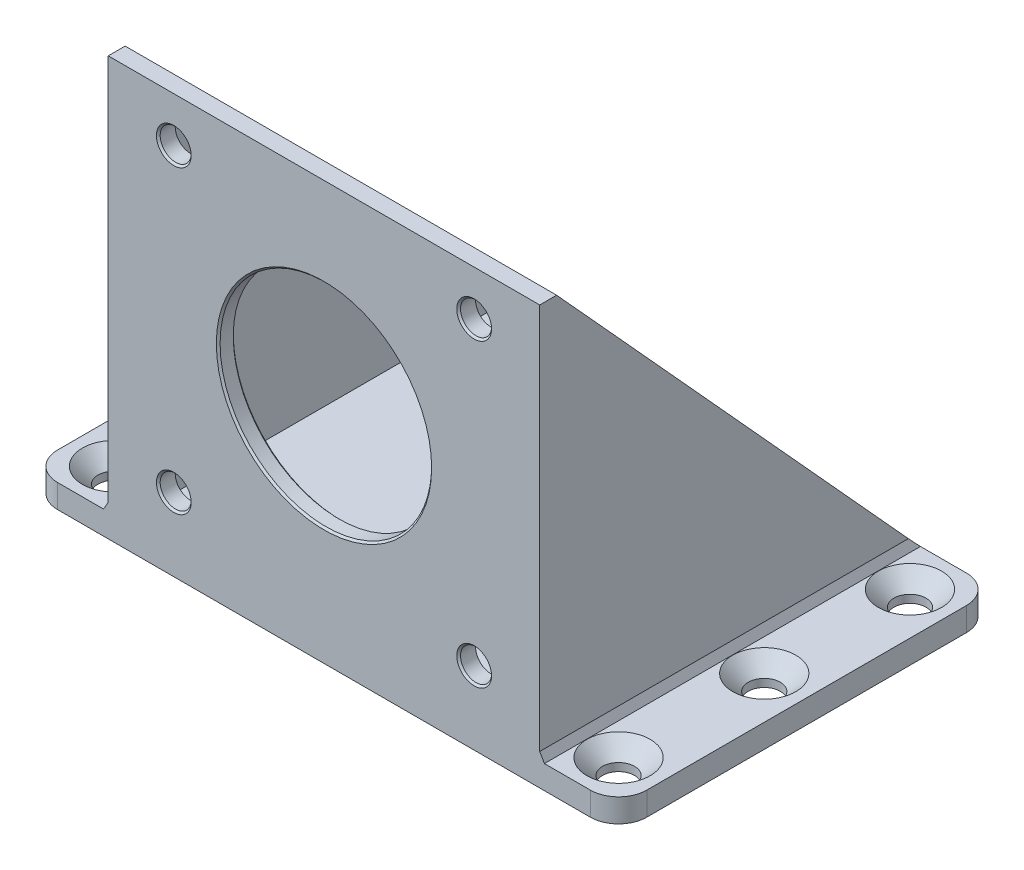
SolidWorks part; units mm, degrees
material "ABS"
ref_plane "Plano frontal" through (0, 0, 0) normal (0, 0, 1) x (1, 0, 0)
ref_plane "Plano superior" through (0, 0, 0) normal (0, 1, 0) x (1, 0, 0)
ref_plane "Plano direito" through (0, 0, 0) normal (1, 0, 0) x (0, 0, -1)
sketch "Esboço1" plane through (0, 0, 0) normal (0, 1, 0) x (1, 0, 0)
  line L1 (-28.335, -20) -> (28.335, -20)
  line L2 (-31.335, -17) -> (-31.335, 17)
  line L3 (-28.335, 20) -> (28.335, 20)
  line L4 (31.335, -17) -> (31.335, 17)
  line L5 (0, 20) -> (0, -20) construction
  line L6 (-31.335, 0) -> (31.335, 0) construction
  arc A0 (28.335, -20) -> (31.335, -17) centre (28.335, -17) ccw
  arc A1 (-31.335, 17) -> (-28.335, 20) centre (-28.335, 17) cw
  arc A2 (-28.335, -20) -> (-31.335, -17) centre (-28.335, -17) cw
  arc A3 (28.335, 20) -> (31.335, 17) centre (28.335, 17) cw
  point P0 (0, 0)
  point P9 (-31.335, 20)
  point P12 (-31.335, -20)
  point P15 (31.335, 20)
  dimension "D3" = 3
  dimension "D1" = 62.67
  dimension "D2" = 40
extrude "Ressalto-extrusão1" add sketch "Esboço1" along normal mid plane 2.5
sketch "Esboço2" plane through (0, 1.25, 0) normal (0, 1, 0) x (1, 0, 0)
  line L0 (-22.95, -20) -> (22.95, -20)
  line L1 (-21.15, 18.2) -> (21.15, 18.2)
  line L2 (-21.15, 18.2) -> (-21.15, -18.2)
  line L3 (-21.15, -18.2) -> (21.15, -18.2)
  line L4 (21.15, 18.2) -> (21.15, -18.2)
  line L5 (0, -18.2) -> (0, 18.2) construction
  line L6 (-21.15, 0) -> (21.15, 0) construction
  line L7 (22.95, 20) -> (22.95, -20)
  line L8 (-22.95, 20) -> (22.95, 20)
  line L9 (-22.95, 20) -> (-22.95, -20)
  line L10 (-28.335, -20) -> (28.335, -20) construction
  line L11 (28.335, 20) -> (-28.335, 20) construction
  point P212 (0, 0)
  dimension "D1" = 42.3
  dimension "D2" = 1.8
extrude "Ressalto-extrusão2" add sketch "Esboço2" along normal blind 42
sketch "Esboço4" plane through (0, 0, 0) normal (1, 0, 0) x (0, 0, -1)
  line L0 (-18.2, 43.25) -> (20, 1.25)
  line L1 (20, 1.25) -> (20, 43.25)
  line L2 (20, 43.25) -> (-18.2, 43.25)
extrude "Corte-extrusão1" cut sketch "Esboço4" against normal through all both and the other way through all
sketch "Esboço5" plane through (0, 0, 20) normal (0, 0, 1) x (1, 0, 0)
  line L6 (-28.335, -1.25) -> (28.335, -1.25) construction
  circle A0 centre (0, 22.5) radius 11.25
  point P2 (0, 0)
  point P6 (0, 0)
  dimension "D1" = 22.5
  dimension "D2" = 23.75
extrude "Corte-extrusão2" cut sketch "Esboço5" against normal through all
sketch "Esboço6" plane through (0, 0, 20) normal (0, 0, 1) x (1, 0, 0)
  line L0 (-15.975, 38.475) -> (15.975, 38.475) construction
  line L1 (-15.975, 38.475) -> (-15.975, 6.525) construction
  line L8 (-22.95, 43.25) -> (-22.95, 1.25) construction
  line L9 (-22.95, 43.25) -> (22.95, 43.25) construction
  circle A0 centre (-15.975, 38.475) radius 1.65
  circle A1 centre (15.975, 38.475) radius 1.65
  circle A2 centre (15.975, 6.525) radius 1.65
  circle A3 centre (-15.975, 6.525) radius 1.65
  point P0 (15.975, 38.475)
  point P15 (-15.975, 38.475)
  dimension "D1" = 3.3
  dimension "D4" = 6.975
  dimension "D5" = 4.775
  dimension "D6" = 31.95
  dimension "D2" = 2
  dimension "D3" = 2
extrude "Corte-extrusão3" cut sketch "Esboço6" against normal through all
sketch "Esboço7" plane through (0, 1.25, 0) normal (0, 1, 0) x (1, 0, 0)
  line L0 (-22.95, 20) -> (22.95, 20) construction
  line L1 (-21.15, 18.2) -> (21.15, 18.2)
  line L2 (-21.15, 18.2) -> (-21.15, 20)
  line L3 (-21.15, 20) -> (21.15, 20)
  line L4 (21.15, 18.2) -> (21.15, 20)
  line L5 (0, 20) -> (0, 18.2) construction
  line L6 (-21.15, 19.1) -> (21.15, 19.1) construction
  point P200 (0, 19.1)
extrude "Corte-extrusão4" cut sketch "Esboço7" along normal through all
hole_wizard "Escareado para SFHCS M31" positions "Esboço8" profile "Esboço9" countersink size "M3" standard "Ansi Metric" end condition through all
sketch "Esboço8" plane through (0, 1.25, 0) normal (0, 1, 0) x (1, 0, 0)
  line L0 (-31.335, 17) -> (-31.335, -17) construction
  line L1 (-28.335, -20) -> (-22.95, -20) construction
  line L2 (-24.475, 0) -> (24.475, 0) construction
  line L3 (0, -22) -> (0, 22) construction
  point P2 (-26.835, 0)
  point P4 (-26.835, -15.5)
  point P22 (-26.835, 15.5)
  point P26 (26.835, 15.5)
  point P27 (26.835, 0)
  point P28 (26.835, -15.5)
  dimension "D1" = 4.5
  dimension "D2" = 4.5
sketch "Esboço9" plane through (-26.835, 1.25, 0) normal (1, 0, 0) x (0, 0, 1)
  line L0 (0, 0) -> (0, 2.5)
  line L1 (0, 2.5) -> (1.7, 2.5)
  line L2 (1.7, 2.5) -> (1.7, 1.66)
  line L3 (1.7, 1.66) -> (3.36, 0)
  line L5 (3.36, 0) -> (0, 0)
  line L6 (-1.7, 1.66) -> (-3.36, 0) construction
  line L11 (0, -6.35) -> (0, 107.95) construction
  dimension "Thru Hole Dia." = 3.4
  dimension "Thru Hole Depth" = 2.5
  dimension "Near C'Sink Dia." = 6.72
  dimension "Near C'Sink Angle" = 90
chamfer "Chanfro1" distance 0.5 angle 60 2 edges at (22.95, 1.25, 0) (-22.95, 1.25, 0)
chamfer "Chanfro2" distance 0.2 angle 45 6 edges at (-14.325, 6.525, 20) (17.625, 6.525, 20) (17.625, 38.475, 20) (-14.325, 38.475, 20) (-11.25, 22.5, 18.2) (11.25, 22.5, 20)
